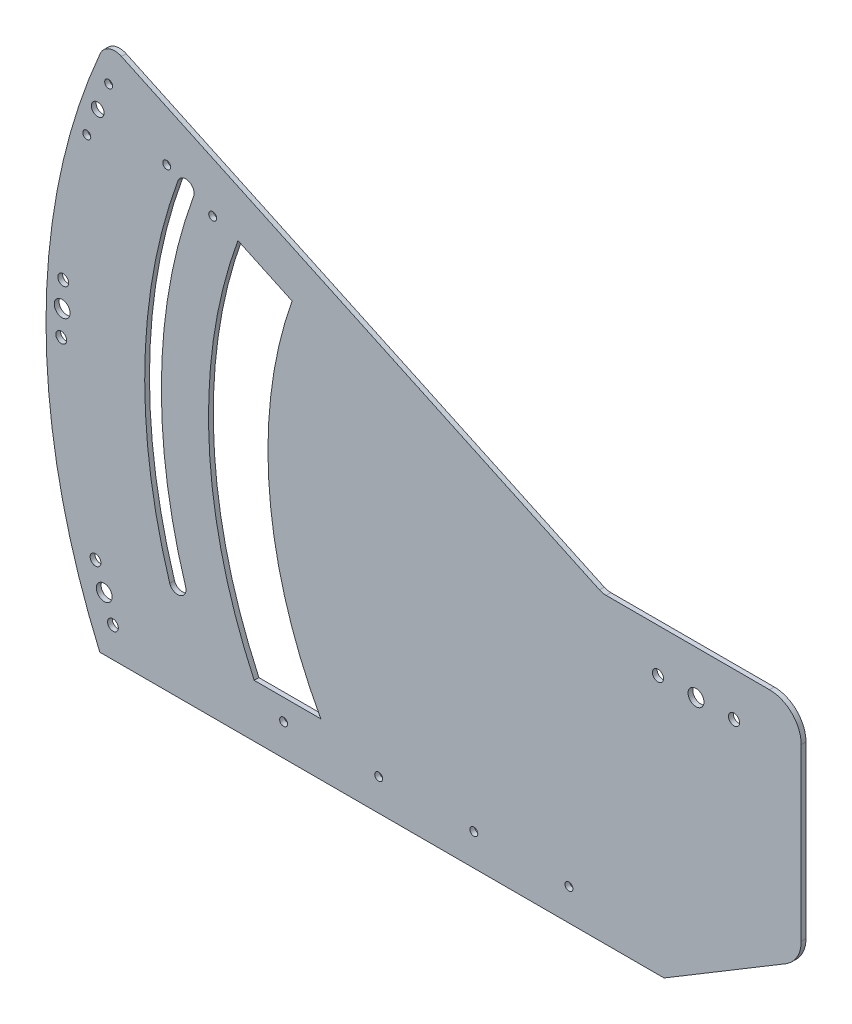
SolidWorks part; units mm, degrees
material "6061 Alloy"
ref_plane "Front Plane" through (0, 0, 0) normal (0, 0, 1) x (1, 0, 0)
ref_plane "Top Plane" through (0, 0, 0) normal (0, 1, 0) x (1, 0, 0)
ref_plane "Right Plane" through (0, 0, 0) normal (1, 0, 0) x (0, 0, -1)
sketch "Sketch1" plane through (0, 0, 0) normal (0, 0, 1) x (1, 0, 0)
  line L0 (0, 0) -> (-350.152, -163.2786) construction
  line L1 (0, 0) -> (-4.5315, 2.1131)
  line L2 (-350.152, -163.2786) -> (-20.152, -163.2786)
  line L4 (0, 0) -> (5, 0)
  line L7 (-56.6931, 27.4702) -> (46.3712, 27.4702)
  line L8 (-60.9192, 28.4071) -> (-362.4098, 168.9945)
  line L11 (-20.152, -163.2786) -> (56.6776, -117.0804)
  line L16 (-376.0852, -163.2786) -> (-350.152, -163.2786)
  line L17 (24, 0) -> (-24, 0) construction
  line L18 (0, 0) -> (-321.8447, 117.1419) construction
  line L24 (0, 0) -> (-391.4042, -122.077) construction
  line L25 (-20.152, -143.2786) -> (-384.15, -143.2786) construction
  line L26 (-288.9555, 105.1712) -> (-254.821, 89.254)
  line L27 (-278.6896, -129.9551) -> (-236.6678, -129.9551)
  line L28 (66.3712, 7.4702) -> (66.3712, -99.9405)
  circle A1 centre (0, 0) radius 65 construction
  circle A2 centre (-176.6092, -55.0835) radius 120 construction
  circle A3 centre (0, 0) radius 185 construction
  circle A4 centre (0, 0) radius 5
  circle A9 centre (-399.8024, 12.5709) radius 5
  circle A10 centre (-373.2848, -129.2214) radius 5
  arc A13 (-56.6931, 27.4702) -> (-60.9192, 28.4071) centre (-56.6931, 37.4702) cw
  circle A16 centre (-400.4035, -3.4047) radius 3.4 construction
  circle A17 centre (-377.3865, 132.5873) radius 4
  arc A22 (-376.0852, -163.2786) -> (-375.8019, 163.9297) centre (0, 0) cw
  arc A23 (-364.8155, -164.0416) -> (-362.5231, 169.0473) centre (0, 0) cw construction
  circle A24 centre (0, 0) radius 342.5 construction
  arc A25 (-320.0114, 122.0614) -> (-310.4104, -144.7468) centre (0, 0) ccw construction
  arc A27 (-321.9538, -100.4157) -> (-316.9113, 115.3463) centre (0, 0) cw
  arc A28 (-331.9776, -103.5421) -> (-326.7781, 118.9375) centre (0, 0) cw
  circle A29 centre (-321.8447, 117.1419) radius 5.25
  arc A30 (-258.8296, 166.0226) -> (-293.5531, -91.5577) centre (0, 0) ccw construction
  arc A31 (-258.8296, 166.0226) -> (-278.6896, -129.9551) centre (0, 0) ccw construction
  circle A37 centre (-399.1543, 28.5709) radius 3.4 construction
  circle A38 centre (-400.4035, -3.4047) radius 3.4
  circle A39 centre (-399.1543, 28.5709) radius 3.4
  circle A40 centre (-367.7832, -144.2458) radius 3.4 construction
  circle A41 centre (-367.7832, -144.2458) radius 3.4
  circle A42 centre (-378.7863, -114.197) radius 3.4 construction
  circle A43 centre (-378.7863, -114.197) radius 3.4
  circle A44 centre (-24, 0) radius 3.5
  circle A45 centre (24, 0) radius 3.5
  arc A46 (-362.4098, 168.9945) -> (-375.8019, 163.9297) centre (-366.636, 159.9314) ccw
  arc A48 (-278.6896, -129.9551) -> (-288.9555, 105.1712) centre (0, 0) cw
  arc A52 (-331.9776, -103.5421) -> (-321.9538, -100.4157) centre (-326.9657, -101.9789) ccw
  arc A53 (-236.6678, -129.9551) -> (-254.821, 89.254) centre (0, 0) cw
  circle A54 centre (-200.152, -143.2786) radius 2.5
  circle A55 centre (-140.152, -143.2786) radius 2.5
  circle A56 centre (-80.152, -143.2786) radius 2.5
  circle A57 centre (-260.152, -143.2786) radius 2.5
  circle A62 centre (-304.8663, 110.537) radius 2.5 construction
  circle A63 centre (-333.8681, 124.0608) radius 2.5 construction
  circle A64 centre (-304.8663, 110.537) radius 2.5
  circle A65 centre (-333.8681, 124.0608) radius 2.5
  arc A66 (66.3712, -99.9405) -> (56.6776, -117.0804) centre (46.3712, -99.9405) cw
  arc A67 (66.3712, 7.4702) -> (46.3712, 27.4702) centre (46.3712, 7.4702) ccw
  circle A71 centre (39.5, 0) radius 14.5 construction
  circle A74 centre (-384.2769, 115.2569) radius 2.5
  circle A75 centre (-370.4961, 149.9178) radius 2.5
  point P25 (66.3712, -111.2516)
  point P35 (-58.91, 27.4702)
  point P83 (66.3712, 27.4702)
  dimension "D2" = 130
  dimension "D3" = 240
  dimension "D5" = 25
  dimension "D7" = 10
  dimension "D9" = 330
  dimension "D10" = 138.7218
  dimension "D12" = 395.0186
  dimension "D13" = 10
  dimension "D14" = 10
  dimension "D15" = 8
  dimension "D16" = 10
  dimension "D17" = 410
  dimension "D18" = 37.322
  dimension "D19" = 45
  dimension "D20" = 48
  dimension "D21" = 7
  dimension "D22" = 5.25
  dimension "D23" = 10
  dimension "D24" = 270
  dimension "D26" = 5
  dimension "D27" = 10
  dimension "D28" = 39.3255
  dimension "D33" = 16
  dimension "D34" = 34.0572
  dimension "D36" = 29
  dimension "D37" = 20
  dimension "D1" = 50
  dimension "D4" = 386.35
  dimension "D8" = 39.5
  dimension "D11" = 100.9607
  dimension "D25" = 20
  dimension "D29" = 60
  dimension "D30" = 60
  dimension "D31" = 60
  dimension "D32" = 60
extrude "Boss-Extrude1" add sketch "Sketch1" along normal blind 3
sketch "Sketch2" plane through (0, 0, 3) normal (0, 0, 1) x (1, 0, 0)
  line L0 (-32.2479, 4.0037) -> (-61.7813, 17.7753)
  line L1 (-123.3082, -42.2814) -> (-118.9632, -12.9942)
  line L2 (-278.6896, -129.9551) -> (-236.6678, -129.9551)
  line L3 (-254.821, 89.254) -> (-288.9555, 105.1712)
  line L4 (-278.6896, -129.9551) -> (-236.6678, -129.9551) construction
  line L5 (-254.821, 89.254) -> (-288.9555, 105.1712) construction
  line L6 (-114.1307, -11.0847) -> (-90.9398, -29.4911)
  line L7 (-91.7023, -34.631) -> (-119.2382, -45.5117)
  line L8 (-94.2374, -75.5682) -> (-117.4283, -57.1618)
  line L9 (-60.9192, 28.4071) -> (-362.4098, 168.9945)
  line L10 (-376.0852, -163.2786) -> (-20.152, -163.2786)
  line L11 (-20.152, -163.2786) -> (56.6776, -117.0804)
  line L12 (66.3712, -99.9405) -> (66.3712, 7.4702)
  line L13 (46.3712, 27.4702) -> (-56.6931, 27.4702)
  line L14 (-60.9192, 28.4071) -> (-362.4098, 168.9945)
  line L15 (-376.0852, -163.2786) -> (-20.152, -163.2786)
  line L16 (-20.152, -163.2786) -> (56.6776, -117.0804)
  line L18 (46.3712, 27.4702) -> (-56.6931, 27.4702)
  line L19 (-116.6658, -52.0219) -> (-89.1299, -41.1412)
  line L20 (-85.0599, -44.3715) -> (-89.4049, -73.6587)
  line L21 (-130.9576, -93.8414) -> (-126.6126, -64.5543)
  line L22 (-121.7801, -62.6447) -> (-98.5892, -81.0512)
  line L23 (-99.3517, -86.191) -> (-126.8876, -97.0717)
  line L24 (-165.1427, -71.1773) -> (-137.6068, -60.2967)
  line L25 (-133.5368, -63.527) -> (-137.8818, -92.8141)
  line L26 (-142.7144, -94.7237) -> (-165.9053, -76.3172)
  line L27 (-162.6077, -30.2401) -> (-139.4168, -48.6466)
  line L28 (-140.1793, -53.7865) -> (-167.7152, -64.6672)
  line L29 (-171.7852, -61.4368) -> (-167.4402, -32.1497)
  line L30 (-125.8875, -11.967) -> (-130.2325, -41.2541)
  line L31 (-135.065, -43.1637) -> (-158.2559, -24.7572)
  line L32 (-157.4934, -19.6173) -> (-129.9575, -8.7366)
  line L33 (-218.734, -100.9556) -> (-195.5431, -119.3621)
  line L34 (-196.3057, -124.502) -> (-223.8416, -135.3826)
  line L35 (-227.9116, -132.1523) -> (-223.5666, -102.8652)
  line L36 (-182.0138, -82.6824) -> (-186.3588, -111.9696)
  line L37 (-191.1914, -113.8792) -> (-214.3823, -95.4727)
  line L38 (-213.6197, -90.3328) -> (-186.0838, -79.4521)
  line L39 (-147.8287, -105.3465) -> (-175.3646, -116.2272)
  line L40 (-179.4346, -112.9969) -> (-175.0896, -83.7097)
  line L41 (-170.257, -81.8002) -> (-147.0661, -100.2066)
  line L51 (-160.2948, 63.7129) -> (-174.9649, 70.5537)
  line L53 (-181.0069, -21.3819) -> (-208.5428, -32.2626)
  line L54 (-212.6128, -29.0323) -> (-208.2678, 0.2549)
  line L55 (-203.4353, 2.1644) -> (-180.2444, -16.242)
  line L56 (-215.192, 1.2821) -> (-219.537, -28.005)
  line L57 (-224.3696, -29.9146) -> (-247.5605, -11.5081)
  line L58 (-246.7979, -6.3682) -> (-219.262, 4.5125)
  line L59 (-183.542, -62.3191) -> (-206.7329, -43.9127)
  line L60 (-205.9703, -38.7728) -> (-178.4344, -27.8921)
  line L61 (-174.3644, -31.1224) -> (-178.7094, -60.4096)
  line L62 (-220.2622, -80.5923) -> (-215.9172, -51.3052)
  line L63 (-211.0846, -49.3956) -> (-187.8937, -67.802)
  line L64 (-188.6563, -72.9419) -> (-216.1922, -83.8226)
  line L65 (-253.5458, -57.572) -> (-226.9114, -47.0476)
  line L66 (-222.8414, -50.2779) -> (-227.1864, -79.565)
  line L67 (-232.019, -81.4746) -> (-251.4751, -66.0324)
  line L68 (-251.9122, -16.991) -> (-228.7213, -35.3975)
  line L69 (-229.4839, -40.5374) -> (-255.0229, -50.629)
  line L70 (-258.3194, -29.5142) -> (-256.7448, -18.9006)
  line L71 (-127.4156, 8.3963) -> (-150.6065, 26.8028)
  line L72 (-149.844, 31.9427) -> (-122.3081, 42.8234)
  line L73 (-118.2381, 39.593) -> (-122.5831, 10.3059)
  line L74 (-127.3584, 48.3544) -> (-152.4165, 38.4529)
  line L75 (-156.4865, 41.6832) -> (-153.6761, 60.6265)
  line L77 (-164.1358, -9.8768) -> (-159.7908, 19.4103)
  line L78 (-154.9583, 21.3199) -> (-131.7674, 2.9134)
  line L79 (-132.5299, -2.2265) -> (-160.0658, -13.1072)
  line L80 (-198.321, 12.7872) -> (-170.7851, 23.6679)
  line L81 (-166.7151, 20.4376) -> (-171.0601, -8.8496)
  line L82 (-175.8926, -10.7591) -> (-199.0835, 7.6473)
  line L83 (-195.7859, 53.7244) -> (-172.595, 35.318)
  line L84 (-173.3575, 30.1781) -> (-200.8934, 19.2974)
  line L85 (-204.9634, 22.5277) -> (-200.6184, 51.8149)
  line L86 (-160.2948, 63.7129) -> (-163.4107, 42.7105)
  line L87 (-168.2432, 40.8009) -> (-191.4341, 59.2074)
  line L88 (-190.6716, 64.3473) -> (-174.9649, 70.5537)
  line L89 (-74.8313, -23.1259) -> (-70.4863, 6.1612)
  line L90 (-65.6537, 8.0708) -> (-42.4628, -10.3357)
  line L91 (-43.2254, -15.4756) -> (-70.7613, -26.3563)
  line L92 (-38.1111, -4.8528) -> (-61.302, 13.5537)
  line L94 (-32.2479, 4.0037) -> (-33.2785, -2.9432)
  line L95 (-109.0164, -0.4619) -> (-81.4805, 10.4188)
  line L96 (-77.4105, 7.1885) -> (-81.7555, -22.0987)
  line L97 (-86.588, -24.0082) -> (-109.7789, -5.6018)
  line L98 (-106.4813, 40.4753) -> (-83.2904, 22.0689)
  line L99 (-84.053, 16.929) -> (-111.5889, 6.0483)
  line L100 (-115.6589, 9.2786) -> (-111.3139, 38.5658)
  line L107 (-75.8382, -84.4265) -> (-48.3023, -73.5458)
  line L108 (-44.2323, -76.7761) -> (-48.5773, -106.0632)
  line L109 (-53.4098, -107.9728) -> (-76.6007, -89.5664)
  line L110 (-41.653, -107.0905) -> (-37.308, -77.8034)
  line L111 (-32.4755, -75.8938) -> (-9.2846, -94.3003)
  line L112 (-10.0471, -99.4402) -> (-37.583, -110.3208)
  line L113 (-73.3031, -43.4892) -> (-50.1122, -61.8957)
  line L114 (-50.8747, -67.0356) -> (-78.4106, -77.9163)
  line L115 (-82.4806, -74.6859) -> (-78.1356, -45.3988)
  line L116 (-36.5829, -25.2161) -> (-40.9279, -54.5032)
  line L117 (-45.7604, -56.4128) -> (-68.9513, -38.0063)
  line L118 (-68.1888, -32.8664) -> (-40.6529, -21.9858)
  line L119 (-2.3978, -47.8801) -> (-29.9337, -58.7608)
  line L120 (-34.0037, -55.5305) -> (-29.6587, -26.2434)
  line L121 (-24.8261, -24.3338) -> (-1.6352, -42.7402)
  line L122 (-4.9328, -88.8174) -> (-28.1237, -70.4109)
  line L123 (-27.3612, -65.271) -> (0.1747, -54.3903)
  line L124 (4.2447, -57.6206) -> (-0.1003, -86.9078)
  line L131 (-92.7092, -95.9316) -> (-97.0542, -125.2187)
  line L132 (-101.8868, -127.1283) -> (-125.0777, -108.7218)
  line L133 (-124.3151, -103.5819) -> (-96.7792, -92.7012)
  line L134 (-58.5241, -118.5956) -> (-86.06, -129.4763)
  line L135 (-90.13, -126.246) -> (-85.785, -96.9588)
  line L136 (-80.9525, -95.0493) -> (-57.7616, -113.4557)
  line L143 (-127.3584, 48.3544) -> (-153.6761, 60.6265)
  line L146 (-56.6931, 37.4702) -> (-200.152, -143.2786) construction
  line L147 (-38.3283, 27.4702) -> (-33.0035, 29.5743)
  line L151 (66.3712, -99.9405) -> (66.3712, 7.4702)
  line L153 (-134.5147, 62.7252) -> (-124.118, 54.4734)
  line L155 (-155.4781, -156.9065) -> (-171.6039, -163.2786)
  line L156 (-128.9514, -163.2786) -> (-132.7271, -160.2818)
  line L161 (-214.1623, -153.2786) -> (-222.0316, -147.0327)
  line L162 (-221.2691, -141.8928) -> (-193.7332, -131.0121)
  line L163 (-189.6632, -134.2425) -> (-192.4874, -153.2786)
  line L164 (-185.4107, -153.2786) -> (-182.739, -135.2697)
  line L165 (-177.9064, -133.3602) -> (-154.7155, -151.7666)
  line L166 (-150.3638, -146.2837) -> (-173.5547, -127.8773)
  line L167 (-141.1862, -115.087) -> (-145.5312, -144.3742)
  line L168 (-107.0011, -137.7511) -> (-134.537, -148.6318)
  line L169 (-138.607, -145.4014) -> (-138.5805, -145.2229)
  line L170 (-172.7921, -122.7374) -> (-145.2562, -111.8567)
  line L171 (-129.4294, -114.2047) -> (-106.2385, -132.6112)
  line L172 (-100.3586, -147.4916) -> (-101.2172, -153.2786)
  line L173 (-127.2489, -153.2786) -> (-104.4286, -144.2612)
  circle A0 centre (-128.4225, -52.9042) radius 3
  circle A1 centre (-24, 0) radius 3.5
  circle A2 centre (-24, 0) radius 3.5 construction
  circle A3 centre (-80.152, -143.2786) radius 2.5
  arc A4 (-288.9555, 105.1712) -> (-278.6896, -129.9551) centre (0, 0) ccw
  arc A5 (-254.821, 89.254) -> (-236.6678, -129.9551) centre (0, 0) ccw
  arc A6 (-288.9555, 105.1712) -> (-278.6896, -129.9551) centre (0, 0) ccw construction
  arc A7 (-254.821, 89.254) -> (-236.6678, -129.9551) centre (0, 0) ccw construction
  circle A8 centre (-80.152, -143.2786) radius 2.5 construction
  circle A9 centre (-140.152, -143.2786) radius 2.5
  circle A10 centre (-140.152, -143.2786) radius 2.5 construction
  circle A11 centre (-200.152, -143.2786) radius 2.5
  circle A12 centre (-200.152, -143.2786) radius 2.5 construction
  arc A13 (-123.3082, -42.2814) -> (-119.2382, -45.5117) centre (-120.3407, -42.7216) ccw
  arc A14 (-90.9398, -29.4911) -> (-91.7023, -34.631) centre (-92.8048, -31.841) cw
  arc A15 (-118.9632, -12.9942) -> (-114.1307, -11.0847) centre (-115.9957, -13.4345) cw
  arc A16 (-89.4049, -73.6587) -> (-94.2374, -75.5682) centre (-92.3724, -73.2184) cw
  arc A17 (-60.9192, 28.4071) -> (-56.6931, 27.4702) centre (-56.6931, 37.4702) ccw
  arc A18 (-362.4098, 168.9945) -> (-375.8019, 163.9297) centre (-366.636, 159.9314) ccw
  arc A19 (-375.8019, 163.9297) -> (-376.0852, -163.2786) centre (0, 0) ccw
  arc A20 (66.3712, 7.4702) -> (46.3712, 27.4702) centre (46.3712, 7.4702) ccw
  arc A21 (56.6776, -117.0804) -> (66.3712, -99.9405) centre (46.3712, -99.9405) ccw
  arc A22 (-60.9192, 28.4071) -> (-56.6931, 27.4702) centre (-56.6931, 37.4702) ccw
  arc A23 (-362.4098, 168.9945) -> (-375.8019, 163.9297) centre (-366.636, 159.9314) ccw
  arc A24 (-375.8019, 163.9297) -> (-376.0852, -163.2786) centre (0, 0) ccw
  arc A25 (66.3712, 7.4702) -> (46.3712, 27.4702) centre (46.3712, 7.4702) ccw
  arc A27 (-116.6658, -52.0219) -> (-117.4283, -57.1618) centre (-115.5633, -54.812) ccw
  arc A28 (-89.1299, -41.1412) -> (-85.0599, -44.3715) centre (-88.0274, -43.9313) cw
  arc A29 (-126.8876, -97.0717) -> (-130.9576, -93.8414) centre (-127.9901, -94.2817) cw
  arc A30 (-121.7801, -62.6447) -> (-126.6126, -64.5543) centre (-123.6451, -64.9945) ccw
  arc A31 (-98.5892, -81.0512) -> (-99.3517, -86.191) centre (-100.4542, -83.401) cw
  arc A32 (-165.9053, -76.3172) -> (-165.1427, -71.1773) centre (-164.0403, -73.9674) cw
  arc A33 (-133.5368, -63.527) -> (-137.6068, -60.2967) centre (-136.5044, -63.0867) ccw
  arc A34 (-137.8818, -92.8141) -> (-142.7144, -94.7237) centre (-140.8494, -92.3739) cw
  arc A35 (-167.4402, -32.1497) -> (-162.6077, -30.2401) centre (-164.4727, -32.59) cw
  arc A36 (-140.1793, -53.7865) -> (-139.4168, -48.6466) centre (-141.2818, -50.9964) ccw
  arc A37 (-167.7152, -64.6672) -> (-171.7852, -61.4368) centre (-168.8177, -61.8771) cw
  arc A38 (-129.9575, -8.7366) -> (-125.8875, -11.967) centre (-128.855, -11.5267) cw
  arc A39 (-135.065, -43.1637) -> (-130.2325, -41.2541) centre (-133.2, -40.8139) ccw
  arc A40 (-158.2559, -24.7572) -> (-157.4934, -19.6173) centre (-156.3909, -22.4074) cw
  arc A41 (-196.3057, -124.502) -> (-195.5431, -119.3621) centre (-197.4081, -121.7119) ccw
  arc A42 (-223.8416, -135.3826) -> (-227.9116, -132.1523) centre (-224.944, -132.5926) cw
  arc A43 (-223.5666, -102.8652) -> (-218.734, -100.9556) centre (-220.599, -103.3054) cw
  arc A44 (-191.1914, -113.8792) -> (-186.3588, -111.9696) centre (-189.3263, -111.5293) ccw
  arc A45 (-214.3823, -95.4727) -> (-213.6197, -90.3328) centre (-212.5172, -93.1229) cw
  arc A46 (-186.0838, -79.4521) -> (-182.0138, -82.6824) centre (-184.9813, -82.2422) cw
  arc A47 (-147.0661, -100.2066) -> (-147.8287, -105.3465) centre (-148.9312, -102.5564) cw
  arc A48 (-179.4346, -112.9969) -> (-175.3646, -116.2272) centre (-176.4671, -113.4371) ccw
  arc A49 (-175.0896, -83.7097) -> (-170.257, -81.8002) centre (-172.1221, -84.15) cw
  circle A59 centre (-184.5489, -123.6197) radius 3
  arc A60 (-258.3194, -29.5142) -> (-255.0229, -50.629) centre (0, 0) ccw
  arc A61 (-212.6128, -29.0323) -> (-208.5428, -32.2626) centre (-209.6453, -29.4725) ccw
  arc A62 (-208.2678, 0.2549) -> (-203.4353, 2.1644) centre (-205.3003, -0.1854) cw
  arc A63 (-180.2444, -16.242) -> (-181.0069, -21.3819) centre (-182.1094, -18.5918) cw
  arc A64 (-224.3696, -29.9146) -> (-219.537, -28.005) centre (-222.5045, -27.5648) ccw
  arc A65 (-247.5605, -11.5081) -> (-246.7979, -6.3682) centre (-245.6955, -9.1583) cw
  arc A66 (-219.262, 4.5125) -> (-215.192, 1.2821) centre (-218.1595, 1.7224) cw
  arc A67 (-205.9703, -38.7728) -> (-206.7329, -43.9127) centre (-204.8679, -41.5629) ccw
  arc A68 (-178.4344, -27.8921) -> (-174.3644, -31.1224) centre (-177.3319, -30.6822) cw
  arc A69 (-178.7094, -60.4096) -> (-183.542, -62.3191) centre (-181.6769, -59.9693) cw
  arc A70 (-211.0846, -49.3956) -> (-215.9172, -51.3052) centre (-212.9497, -51.7454) ccw
  arc A71 (-187.8937, -67.802) -> (-188.6563, -72.9419) centre (-189.7588, -70.1519) cw
  arc A72 (-216.1922, -83.8226) -> (-220.2622, -80.5923) centre (-217.2947, -81.0326) cw
  arc A73 (-222.8414, -50.2779) -> (-226.9114, -47.0476) centre (-225.8089, -49.8376) ccw
  arc A74 (-227.1864, -79.565) -> (-232.019, -81.4746) centre (-230.1539, -79.1248) cw
  arc A76 (-229.4839, -40.5374) -> (-228.7213, -35.3975) centre (-230.5864, -37.7473) ccw
  arc A78 (-256.7448, -18.9006) -> (-251.9122, -16.991) centre (-253.7773, -19.3408) cw
  circle A79 centre (-217.7271, -39.6551) radius 3
  arc A80 (-149.844, 31.9427) -> (-150.6065, 26.8028) centre (-148.7415, 29.1526) ccw
  arc A81 (-122.3081, 42.8234) -> (-118.2381, 39.593) centre (-121.2056, 40.0333) cw
  arc A82 (-122.5831, 10.3059) -> (-127.4156, 8.3963) centre (-125.5506, 10.7462) cw
  arc A83 (-156.4865, 41.6832) -> (-152.4165, 38.4529) centre (-153.5189, 41.2429) ccw
  arc A86 (-154.9583, 21.3199) -> (-159.7908, 19.4103) centre (-156.8233, 18.9701) ccw
  arc A87 (-131.7674, 2.9134) -> (-132.5299, -2.2265) centre (-133.6324, 0.5636) cw
  arc A88 (-160.0658, -13.1072) -> (-164.1358, -9.8768) centre (-161.1683, -10.3171) cw
  arc A89 (-166.7151, 20.4376) -> (-170.7851, 23.6679) centre (-169.6826, 20.8778) ccw
  arc A90 (-171.0601, -8.8496) -> (-175.8926, -10.7591) centre (-174.0276, -8.4093) cw
  arc A91 (-199.0835, 7.6473) -> (-198.321, 12.7872) centre (-197.2185, 9.9972) cw
  arc A92 (-173.3575, 30.1781) -> (-172.595, 35.318) centre (-174.46, 32.9682) ccw
  arc A93 (-200.8934, 19.2974) -> (-204.9634, 22.5277) centre (-201.9959, 22.0875) cw
  arc A94 (-200.6184, 51.8149) -> (-195.7859, 53.7244) centre (-197.6509, 51.3746) cw
  arc A95 (-168.2432, 40.8009) -> (-163.4107, 42.7105) centre (-166.3782, 43.1507) ccw
  arc A96 (-191.4341, 59.2074) -> (-190.6716, 64.3473) centre (-189.5691, 61.5572) cw
  circle A98 centre (-161.6008, 31.0604) radius 3
  arc A99 (-65.6537, 8.0708) -> (-70.4863, 6.1612) centre (-67.5187, 5.721) ccw
  arc A100 (-42.4628, -10.3357) -> (-43.2254, -15.4756) centre (-44.3278, -12.6855) cw
  arc A101 (-70.7613, -26.3563) -> (-74.8313, -23.1259) centre (-71.8637, -23.5662) cw
  arc A102 (-61.7813, 17.7753) -> (-61.302, 13.5537) centre (-59.4369, 15.9035) ccw
  arc A104 (-33.2785, -2.9432) -> (-38.1111, -4.8528) centre (-36.246, -2.5029) cw
  arc A105 (-77.4105, 7.1885) -> (-81.4805, 10.4188) centre (-80.378, 7.6287) ccw
  arc A106 (-81.7555, -22.0987) -> (-86.588, -24.0082) centre (-84.723, -21.6584) cw
  arc A107 (-109.7789, -5.6018) -> (-109.0164, -0.4619) centre (-107.9139, -3.252) cw
  arc A108 (-84.053, 16.929) -> (-83.2904, 22.0689) centre (-85.1554, 19.7191) ccw
  arc A109 (-111.5889, 6.0483) -> (-115.6589, 9.2786) centre (-112.6913, 8.8384) cw
  arc A110 (-111.3139, 38.5658) -> (-106.4813, 40.4753) centre (-108.3463, 38.1255) cw
  circle A117 centre (-72.2962, 17.8113) radius 3
  arc A118 (-44.2323, -76.7761) -> (-48.3023, -73.5458) centre (-47.1998, -76.3358) ccw
  arc A119 (-48.5773, -106.0632) -> (-53.4098, -107.9728) centre (-51.5448, -105.623) cw
  arc A120 (-76.6007, -89.5664) -> (-75.8382, -84.4265) centre (-74.7357, -87.2165) cw
  arc A121 (-32.4755, -75.8938) -> (-37.308, -77.8034) centre (-34.3405, -78.2436) ccw
  arc A122 (-9.2846, -94.3003) -> (-10.0471, -99.4402) centre (-11.1496, -96.6501) cw
  arc A123 (-37.583, -110.3208) -> (-41.653, -107.0905) centre (-38.6855, -107.5308) cw
  arc A124 (-50.8747, -67.0356) -> (-50.1122, -61.8957) centre (-51.9772, -64.2455) ccw
  arc A125 (-78.4106, -77.9163) -> (-82.4806, -74.6859) centre (-79.5131, -75.1262) cw
  arc A126 (-78.1356, -45.3988) -> (-73.3031, -43.4892) centre (-75.1681, -45.8391) cw
  arc A127 (-45.7604, -56.4128) -> (-40.9279, -54.5032) centre (-43.8954, -54.063) ccw
  arc A128 (-68.9513, -38.0063) -> (-68.1888, -32.8664) centre (-67.0863, -35.6565) cw
  arc A129 (-40.6529, -21.9858) -> (-36.5829, -25.2161) centre (-39.5504, -24.7758) cw
  arc A130 (-34.0037, -55.5305) -> (-29.9337, -58.7608) centre (-31.0362, -55.9707) ccw
  arc A131 (-29.6587, -26.2434) -> (-24.8261, -24.3338) centre (-26.6911, -26.6836) cw
  arc A132 (-1.6352, -42.7402) -> (-2.3978, -47.8801) centre (-3.5002, -45.0901) cw
  arc A133 (-27.3612, -65.271) -> (-28.1237, -70.4109) centre (-26.2587, -68.0611) ccw
  arc A134 (0.1747, -54.3903) -> (4.2447, -57.6206) centre (1.2772, -57.1804) cw
  arc A135 (-0.1003, -86.9078) -> (-4.9328, -88.8174) centre (-3.0678, -86.4675) cw
  circle A136 centre (-39.118, -66.1533) radius 3
  arc A143 (-101.8868, -127.1283) -> (-97.0542, -125.2187) centre (-100.0218, -124.7784) ccw
  arc A144 (-125.0777, -108.7218) -> (-124.3151, -103.5819) centre (-123.2127, -106.372) cw
  arc A145 (-96.7792, -92.7012) -> (-92.7092, -95.9316) centre (-95.6768, -95.4913) cw
  arc A146 (-90.13, -126.246) -> (-86.06, -129.4763) centre (-87.1625, -126.6862) ccw
  arc A147 (-85.785, -96.9588) -> (-80.9525, -95.0493) centre (-82.8175, -97.3991) cw
  arc A148 (-57.7616, -113.4557) -> (-58.5241, -118.5956) centre (-59.6266, -115.8055) cw
  circle A155 centre (-95.2443, -136.8688) radius 3
  arc A156 (-124.118, 54.4734) -> (-124.8806, 49.3336) centre (-125.983, 52.1236) cw
  arc A158 (-152.1415, 70.9703) -> (-147.3089, 72.8799) centre (-149.1739, 70.5301) cw
  arc A162 (-28.9805, 27.4702) -> (-28.9335, 26.3439) centre (-31.901, 26.7842) cw
  arc A164 (56.6776, -117.0804) -> (66.3712, -99.9405) centre (46.3712, -99.9405) ccw
  arc A166 (-104.7036, -176.7787) -> (-109.5362, -178.6883) centre (-107.6711, -176.3385) cw
  arc A169 (-194.0082, -163.5296) -> (-198.8407, -165.4392) centre (-196.9757, -163.0894) cw
  arc A170 (-183.014, -167.7872) -> (-187.084, -164.5569) centre (-184.1164, -164.9971) cw
  arc A171 (-132.7271, -160.2818) -> (-131.9645, -155.1419) centre (-130.862, -157.932) cw
  arc A172 (-245.3831, 85.9483) -> (-227.9024, -125.142) centre (0, 0) ccw construction
  arc A173 (-253.5458, -57.572) -> (-251.4751, -66.0324) centre (0, 0) ccw
  arc A174 (-222.0316, -147.0327) -> (-221.2691, -141.8928) centre (-220.1666, -144.6829) cw
  arc A175 (-189.6632, -134.2425) -> (-190.7657, -131.4524) centre (-192.6307, -133.8022) ccw
  arc A176 (-177.9064, -133.3602) -> (-182.739, -135.2697) centre (-179.7714, -135.71) ccw
  arc A177 (-154.7155, -151.7666) -> (-153.6999, -153.2786) centre (-156.5805, -154.1164) cw
  arc A178 (-134.537, -148.6318) -> (-138.607, -145.4014) centre (-135.6395, -145.8417) cw
  arc A179 (-145.5312, -144.3742) -> (-150.3638, -146.2837) centre (-148.4987, -143.9339) cw
  arc A180 (-145.2562, -111.8567) -> (-141.1862, -115.087) centre (-144.1537, -114.6468) cw
  arc A181 (-172.7921, -122.7374) -> (-173.5547, -127.8773) centre (-171.6896, -125.5274) ccw
  arc A182 (-134.262, -116.1143) -> (-129.4294, -114.2047) centre (-131.2945, -116.5545) cw
  arc A183 (-107.0011, -137.7511) -> (-106.2385, -132.6112) centre (-108.1036, -134.961) ccw
  arc A184 (-100.3586, -147.4916) -> (-104.4286, -144.2612) centre (-103.3261, -147.0513) ccw
  point P42 (-124.0708, -47.4213)
  point P45 (-86.8698, -32.7215)
  point P93 (-128.4225, -52.9042)
  point P437 (-128.4225, -52.9042)
  dimension "D7" = 6
  dimension "D10" = 3
  dimension "D8" = 2
  dimension "D9" = 40
  dimension "D12" = 7
  dimension "D13" = 7
  dimension "D16" = 7
  dimension "D17" = 7
  dimension "D18" = 10
  dimension "D1" = 0
  dimension "D2" = 0
  dimension "D3" = 0
  dimension "D4" = 0
  dimension "D5" = 0
  dimension "D6" = 0
  dimension "D14" = 10
  dimension "D11" = 6
  dimension "D15" = 6
extrude "Cut-Extrude1" [suppressed] cut sketch "Sketch2" against normal up to surface (3 mm away) contours A96 L87 A95 L86 L51 L88 | L75 A83 L74 L143 | A82 L73 A81 L72 A80 L71 | A110 L100 A109 L99 A108 L98 | A117 | A132 L121 A131 L120 A130 L119 | A135 L124 A134 L123 A133 L122 | A123 L112 A122 L111 A121 L110 | A120 L109 A119 L108 A118 L107 | A148 L136 A147 L135 A146 L134 | A145 L133 A144 L132 A143 L131 | A49 L40 A48 L39 A47 L41 | A46 L38 A45 L37 A44 L36 | A43 L35 A42 L34 A41 L33 | A72 L64 A71 L63 A70 L62 | L65 A173 L67 A74 L66 A73 | A78 L70 A60 L69 A76 L68 | A66 L58 A65 L57 A64 L56 | A63 L55 A62 L54 A61 L53 | A91 L82 A90 L81 A89 L80 | A98 | A88 L79 A87 L78 A86 L77 | A69 L61 A68 L60 A67 L59 | A37 L28 A36 L27 A35 L29 | A40 L31 A39 L30 A38 L32 | A15 L1 A13 L7 A14 L6 | A107 L97 A106 L96 A105 L95 | A101 L91 A100 L90 A99 L89 | A129 L118 A128 L117 A127 L116 | A126 L115 A125 L114 A124 L113 | A28 L19 A27 L8 A16 L20 | A31 L22 A30 L21 A29 L23 | A34 L25 A33 L24 A32 L26 | A79 | A0 | A136 | L85 A94 L83 A92 L84 A93
